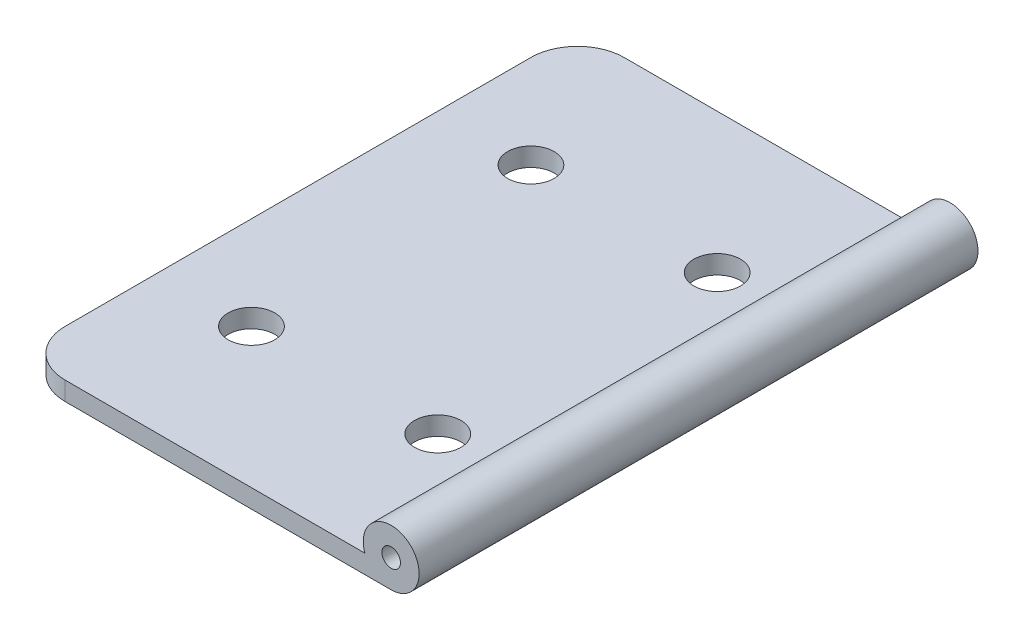
SolidWorks part; units mm, degrees
ref_plane "Front Plane" through (0, 0, 0) normal (0, 0, 1) x (1, 0, 0)
ref_plane "Top Plane" through (0, 0, 0) normal (0, 1, 0) x (1, 0, 0)
ref_plane "Right Plane" through (0, 0, 0) normal (1, 0, 0) x (0, 0, -1)
sketch "Sketch1" plane through (0, 0, 0) normal (0, 1, 0) x (1, 0, 0)
  line L0 (-32.5714, 0) -> (50.2857, 0) construction
  line L1 (0, 66.5714) -> (0, -65.7143) construction
  line L2 (-40, 30) -> (0, 30)
  line L3 (-40, 30) -> (-40, -30)
  line L4 (-40, -30) -> (0, -30)
  line L5 (0, 30) -> (0, -30)
  line L6 (-40, 30) -> (0, -30) construction
  line L7 (-40, -30) -> (0, 30) construction
  line L8 (-20, 30) -> (-20, -30) construction
  circle A0 centre (-30, 15) radius 2.5
  circle A1 centre (-10, 15) radius 2.5
  circle A2 centre (-10, -15) radius 2.5
  circle A3 centre (-30, -15) radius 2.5
  point P1 (-20, 0)
  dimension "D4" = 5
  dimension "D1" = 40
  dimension "D2" = 60
  dimension "D3" = 20
extrude "Boss-Extrude1" add sketch "Sketch1" along normal blind 2
fillet "Fillet1" radius 5 2 edges at (-40, 1, -30) (-40, 1, 30)
sketch "Sketch2" plane through (0, 0, 30) normal (0, 0, 1) x (1, 0, 0)
  line L0 (0, 3) -> (0, 2) construction
  line L1 (0, 2) -> (0, 0) construction
  circle A0 centre (0, 3) radius 3
  circle A1 centre (0, 3) radius 1
  dimension "D1" = 2
extrude "Boss-Extrude2" add sketch "Sketch2" against normal up to surface (60 mm away) up to face at (-17.5, 1, -30)
sketch "Sketch3" [suppressed] plane through (0, 0, 0) normal (0, -1, 0) x (1, 0, 0)
  line L0 (3, 0) -> (-40, 0) construction
  line L1 (3, -30) -> (3, 30) construction
  line L2 (-40, -25) -> (-40, 25) construction
  line L3 (3, 20) -> (-40, 20)
  line L4 (-35, 30) -> (0, 30) construction
  line L5 (3, -20) -> (-40, -20)
  line L7 (-3, -30) -> (3, -30)
  line L8 (-3, -30) -> (-3, 30)
  line L9 (-3, 30) -> (3, 30)
  line L10 (3, -30) -> (3, 30)
  line L11 (-3, -30) -> (3, 30) construction
  line L12 (-3, 30) -> (3, -30) construction
  point P12 (0, 0)
  dimension "D1" = 10
extrude "Cut-Extrude2" [suppressed] cut sketch "Sketch3" against normal up to next contours L8 L5 L7 L3 | L5 L10 L3 L7
sketch "Sketch4" [suppressed] plane through (0, 0, 0) normal (0, -1, 0) x (1, 0, 0)
  line L0 (3, 19.5) -> (-40, 19.5)
  line L1 (-3, -30) -> (3, -30)
  line L2 (-3, -30) -> (-3, 30)
  line L3 (-3, 30) -> (3, 30)
  line L4 (3, -30) -> (3, 30)
  line L5 (-3, -30) -> (3, 30) construction
  line L6 (-3, 30) -> (3, -30) construction
  line L7 (-40, -25) -> (-40, 25) construction
  line L8 (-35, 30) -> (0, 30) construction
  line L9 (-40, 0) -> (3, 0) construction
  line L10 (3, -19.5) -> (-40, -19.5)
  point P0 (0, 0)
  line M5 (-35, -30) -> (0, -30)
  line M6 (0, -30) -> (0, 30)
  line M7 (0, 30) -> (-35, 30)
  dimension "D1" = 10.5
extrude "Cut-Extrude3" [suppressed] cut sketch "Sketch4" against normal up to next contours L2 L0 M6 M7 | L0 L4 L3 M6 | L10 L2 M6 M5 | L4 L10 L1 M6
ref_plane "Mount plane" through (-3, 0, 0) normal (-1, 0, 0) x (0, 0, 1)
